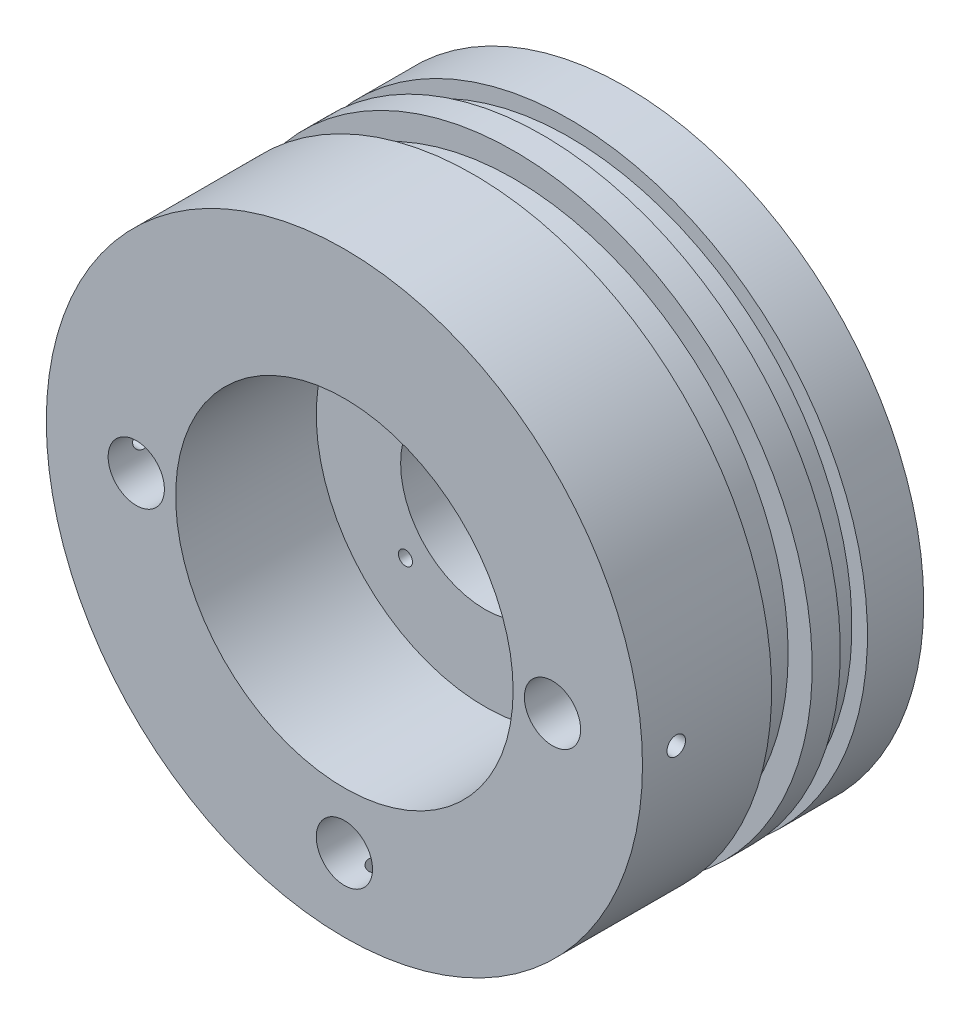
SolidWorks part; units mm, degrees
material "1060 Alloy"
ref_plane "Front Plane" through (0, 0, 0) normal (0, 0, 1) x (1, 0, 0)
ref_plane "Top Plane" through (0, 0, 0) normal (0, 1, 0) x (1, 0, 0)
ref_plane "Right Plane" through (0, 0, 0) normal (1, 0, 0) x (0, 0, -1)
sketch "Sketch1" plane through (0, 0, 0) normal (0, 0, 1) x (1, 0, 0)
  circle A0 centre (0, 0) radius 53
  dimension "D1" = 106
extrude "Boss-Extrude1" add sketch "Sketch1" along normal blind 50
hole_wizard "Ø10.0 (10) Diameter Hole1" positions "Sketch7" profile "Sketch9" hole size "Ø10.0" standard "ISO"
sketch "Sketch7" plane through (0, 0, 50) normal (0, 0, 1) x (1, 0, 0)
  point P0 (-37, 0)
  point P2 (37, 0)
  point P4 (0, -40)
  dimension "D1" = 37
  dimension "D2" = 37
  dimension "D3" = 40
sketch "Sketch9" plane through (-37, 0, 50) normal (1, 0, 0) x (0, -1, 0)
  line L0 (0, 0) -> (0, 20.5043)
  line L1 (0, 20.5043) -> (5, 17.5)
  line L2 (5, 17.5) -> (5, 0)
  line L5 (5, 0) -> (0, 0)
  line L10 (0, 20.5043) -> (-5, 17.5) construction
  line L11 (0, -6.35) -> (0, 107.95) construction
  dimension "Hole Dia." = 10
  dimension "Hole Depth" = 17.5
  dimension "Drill Angle" = 118
ref_plane "Plane1" through (-53, 0, 0) normal (-1, 0, 0) x (0, 0, 1)
hole_wizard "M4 Tapped Hole1" positions "Sketch4" profile "Sketch5" tap size "M4" standard "ISO"
sketch "Sketch4" plane through (-53, 0, 0) normal (-1, 0, 0) x (0, 0, 1)
  line L0 (50, -53) -> (50, 53) construction
  point P0 (44, 0)
  dimension "D1" = 6
sketch "Sketch5" plane through (-53, 0, 44) normal (0, 1, 0) x (0, 0, 1)
  line L0 (0, 0) -> (0, 85)
  line L1 (0, 85) -> (1.65, 85)
  line L2 (1.65, 85) -> (1.65, 0)
  line L5 (1.65, 0) -> (0, 0)
  line L11 (0, -6.35) -> (0, 107.95) construction
  dimension "Thru Tap Drill Dia." = 3.3
  dimension "Thru Tap Drill Depth" = 85
cosmetic thread "Hole Thread1" parameters "D2"=4
pattern_circular "CirPattern1" count 3 every 90 about axis through (0, 0, 50) along (0, 0, 1) of "M4 Tapped Hole1"
sketch "Sketch11" plane through (0, 0, 50) normal (0, 0, 1) x (1, 0, 0)
  circle A0 centre (0, 0) radius 30
  dimension "D1" = 60
extrude "Cut-Extrude2" cut sketch "Sketch11" against normal blind 25
sketch "Sketch12" plane through (0, 0, 0) normal (1, 0, 0) x (0, 0, -1)
  line L0 (0, 53) -> (-50, 53) construction
  line L1 (-10, 53) -> (-14.826, 53)
  line L2 (-10, 53) -> (-10, 50.2348)
  line L3 (-10, 50.2348) -> (-14.826, 50.2348)
  line L4 (-14.826, 53) -> (-14.826, 50.2348)
  line L5 (0, -53) -> (0, 53) construction
  line L6 (0, 0) -> (-18.8162, 0) construction
  line L8 (-19.826, 53) -> (-27.0396, 53)
  line L9 (-19.826, 53) -> (-19.826, 48.7274)
  line L10 (-19.826, 48.7274) -> (-27.0396, 48.7274)
  line L11 (-27.0396, 53) -> (-27.0396, 48.7274)
  point P14 (-19.826, 50.8637)
  dimension "D1" = 10
  dimension "D2" = 4.826
  dimension "D3" = 50.2348
  dimension "D4" = 7.2136
  dimension "D5" = 5
  dimension "D6" = 48.7274
revolve "Cut-Revolve1" cut sketch "Sketch12" angle 360 about L6
sketch "Sketch14" plane through (0, 0, 0) normal (1, 0, 0) x (0, 0, -1)
  line L0 (0, -53) -> (0, 53) construction
  line L1 (0, 27.1526) -> (-2.667, 27.1526)
  line L2 (0, 27.1526) -> (0, 22.5806)
  line L3 (0, 22.5806) -> (-2.667, 22.5806)
  line L4 (-2.667, 27.1526) -> (-2.667, 22.5806)
  line L6 (0, 0) -> (21.0083, 0) construction
  dimension "D1" = 2.667
  dimension "D2" = 4.572
  dimension "D3" = 22.5806
revolve "Cut-Revolve2" cut sketch "Sketch14" angle 360 about L6
sketch "Sketch15" plane through (0, 0, 0) normal (0, 0, -1) x (-1, 0, 0)
  circle A3 centre (0, 0) radius 15
  dimension "D6" = 30
extrude "Cut-Extrude3" cut sketch "Sketch15" against normal up to next
hole_wizard "M5 Tapped Hole1" positions "Sketch16" profile "Sketch17" tap size "M5" standard "ISO"
sketch "Sketch16" plane through (0, 0, 0) normal (0, 0, -1) x (-1, 0, 0)
  line L0 (0, 0) -> (28.2843, 28.2843) construction
  line L3 (0, 0) -> (0, 39.1182) construction
  point P0 (28.2843, 28.2843)
  dimension "D1" = 45
  dimension "D2" = 40
sketch "Sketch17" plane through (-28.2843, 28.2843, 0) normal (1, 0, 0) x (0, 1, 0)
  line L0 (0, 0) -> (0, 15.2618)
  line L1 (0, 15.2618) -> (2.1, 14)
  line L2 (2.1, 14) -> (2.1, 0)
  line L5 (2.1, 0) -> (0, 0)
  line L10 (0, 15.2618) -> (-2.1, 14) construction
  line L11 (0, -6.35) -> (0, 107.95) construction
  dimension "Tap Drill Dia." = 4.2
  dimension "Tap Drill Depth" = 14
  dimension "Drill Angle" = 118
cosmetic thread "Hole Thread5" parameters "D1"=10, "D2"=5
pattern_circular "CirPattern2" count 8 over 360 about axis through (0, 0, 0) along (0, 0, 1) of "M5 Tapped Hole1"
hole_wizard "M3 Tapped Hole1" positions "Sketch18" profile "Sketch19" tap size "M3" standard "ISO"
sketch "Sketch18" plane through (0, 0, 25) normal (0, 0, 1) x (1, 0, 0)
  line L0 (0, 0) -> (14.1421, 14.1421) construction
  line L3 (0, 0) -> (22.4263, 0) construction
  point P0 (14.1421, 14.1421)
  dimension "D1" = 20
  dimension "D3" = 45
sketch "Sketch19" plane through (14.1421, 14.1421, 25) normal (1, 0, 0) x (0, -1, 0)
  line L0 (0, 0) -> (0, 8.2511)
  line L1 (0, 8.2511) -> (1.25, 7.5)
  line L2 (1.25, 7.5) -> (1.25, 0)
  line L5 (1.25, 0) -> (0, 0)
  line L10 (0, 8.2511) -> (-1.25, 7.5) construction
  line L11 (0, -6.35) -> (0, 107.95) construction
  dimension "Tap Drill Dia." = 2.5
  dimension "Tap Drill Depth" = 7.5
  dimension "Drill Angle" = 118
cosmetic thread "Hole Thread6" parameters "D1"=6, "D2"=3
pattern_circular "CirPattern3" count 4 over 360 about axis through (0, 0, 0) along (0, 0, 1) of "M3 Tapped Hole1"
equation "\"3.995هى\"=42.5"
